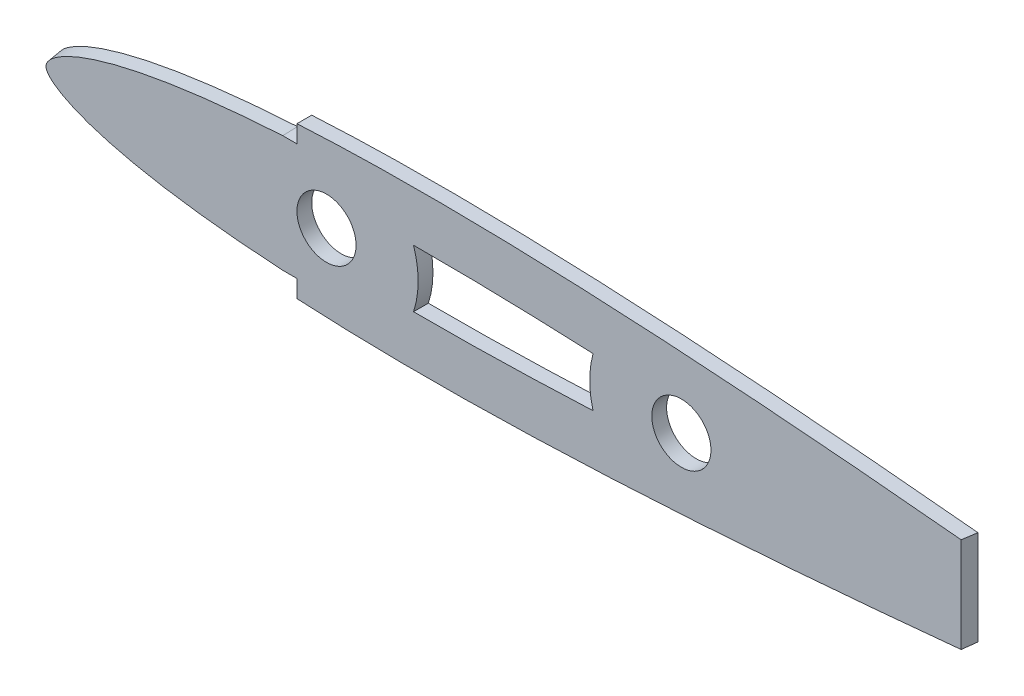
SolidWorks part; units mm, degrees
material "Balsa"
ref_plane "Front Plane" through (0, 0, 0) normal (0, 0, 1) x (1, 0, 0)
ref_plane "Top Plane" through (0, 0, 0) normal (0, 1, 0) x (1, 0, 0)
ref_plane "Right Plane" through (0, 0, 0) normal (1, 0, 0) x (0, 0, -1)
curve "Curve1"
  spline degree 3 poles (283.1769, -0.4783, 0) (283.1769, 0.4783, 0) (282.223, 0.3615, 0) (281.0143, 0.7018, 0) (278.7977, 0.9121, 0) (275.8116, 1.3634, 0) (271.9651, 1.8671, 0) (267.3264, 2.4878, 0) (261.9077, 3.1895, 0) (255.7482, 3.9707, 0) (248.8838, 4.8179, 0) (241.3575, 5.7194, 0) (233.2156, 6.6641, 0) (224.5081, 7.6392, 0) (215.289, 8.6327, 0) (205.6149, 9.6324, 0) (195.5456, 10.6252, 0) (185.1431, 11.5974, 0) (174.4716, 12.536, 0) (163.5969, 13.4255, 0) (152.5858, 14.2512, 0) (141.5064, 14.998, 0) (130.4269, 15.6501, 0) (119.4155, 16.1911, 0) (108.5401, 16.6066, 0) (97.8677, 16.883, 0) (87.464, 17.0069, 0) (77.3931, 16.9683, 0) (67.717, 16.7598, 0) (58.4953, 16.3762, 0) (49.7847, 15.8164, 0) (41.6389, 15.0822, 0) (34.1075, 14.1792, 0) (27.2365, 13.1151, 0) (21.0677, 11.9011, 0) (15.637, 10.5509, 0) (10.9755, 9.0777, 0) (7.1067, 7.4951, 0) (4.043, 5.8139, 0) (1.7891, 4.0308, 0) (0.3455, 2.1026, 0) (-0.161, 0, 0) (0.3455, -2.1026, 0) (1.7891, -4.0308, 0) (4.043, -5.8139, 0) (7.1067, -7.4951, 0) (10.9755, -9.0777, 0) (15.637, -10.5509, 0) (21.0677, -11.9011, 0) (27.2365, -13.1151, 0) (34.1075, -14.1792, 0) (41.6389, -15.0822, 0) (49.7847, -15.8164, 0) (58.4953, -16.3762, 0) (67.717, -16.7598, 0) (77.3931, -16.9683, 0) (87.464, -17.0069, 0) (97.8677, -16.883, 0) (108.5401, -16.6066, 0) (119.4155, -16.1911, 0) (130.4269, -15.6501, 0) (141.5064, -14.998, 0) (152.5858, -14.2512, 0) (163.5969, -13.4255, 0) (174.4716, -12.536, 0) (185.1431, -11.5974, 0) (195.5456, -10.6252, 0) (205.6149, -9.6324, 0) (215.289, -8.6327, 0) (224.5081, -7.6392, 0) (233.2156, -6.6641, 0) (241.3575, -5.7194, 0) (248.8838, -4.8179, 0) (255.7482, -3.9707, 0) (261.9077, -3.1895, 0) (267.3264, -2.4878, 0) (271.9651, -1.8671, 0) (275.8116, -1.3634, 0) (278.7977, -0.9121, 0) (281.0143, -0.7018, 0) (282.223, -0.3615, 0) (283.1769, -0.4783, 0) (283.1769, 0.4783, 0) (282.223, 0.3615, 0) knots -0.004279 -0.001997 -0.001234 0 0.000762 0.003045 0.006832 0.012101 0.018818 0.026939 0.036415 0.047185 0.05918 0.072328 0.086544 0.101741 0.117823 0.134691 0.15224 0.170361 0.188941 0.207865 0.227016 0.246276 0.265525 0.284645 0.30352 0.322035 0.340078 0.357543 0.374325 0.39033 0.405464 0.419644 0.432793 0.444844 0.455738 0.465429 0.473886 0.481102 0.487102 0.491975 0.495931 0.499383 0.502835 0.50679 0.511664 0.517664 0.524879 0.533337 0.543028 0.553922 0.565972 0.579122 0.593302 0.608436 0.62444 0.641223 0.658687 0.676731 0.695245 0.714121 0.733241 0.75249 0.77175 0.7909 0.809825 0.828404 0.846525 0.864074 0.880942 0.897025 0.912222 0.926438 0.939585 0.951581 0.962351 0.971826 0.979948 0.986664 0.991933 0.995721 0.998003 0.998766 1 1.000762 1.003045 1.006832 periodic
sketch "Sketch1" plane through (0, 0, 0) normal (0, 0, 1) x (1, 0, 0)
  spline S0 degree 3 poles (283.1769, -0.4783) (283.1769, 0.4783) (282.223, 0.3615) (281.0143, 0.7018) (278.7977, 0.9121) (275.8116, 1.3634) (271.9651, 1.8671) (267.3264, 2.4878) (261.9077, 3.1895) (255.7482, 3.9707) (248.8838, 4.8179) (241.3575, 5.7194) (233.2156, 6.6641) (224.5081, 7.6392) (215.289, 8.6327) (205.6149, 9.6324) (195.5456, 10.6252) (185.1431, 11.5974) (174.4716, 12.536) (163.5969, 13.4255) (152.5858, 14.2512) (141.5064, 14.998) (130.4269, 15.6501) (119.4155, 16.1911) (108.5401, 16.6066) (97.8677, 16.883) (87.464, 17.0069) (77.3931, 16.9683) (67.717, 16.7598) (58.4953, 16.3762) (49.7847, 15.8164) (41.6389, 15.0822) (34.1075, 14.1792) (27.2365, 13.1151) (21.0677, 11.9011) (15.637, 10.5509) (10.9755, 9.0777) (7.1067, 7.4951) (4.043, 5.8139) (1.7891, 4.0308) (0.3455, 2.1026) (-0.161, 0) (0.3455, -2.1026) (1.7891, -4.0308) (4.043, -5.8139) (7.1067, -7.4951) (10.9755, -9.0777) (15.637, -10.5509) (21.0677, -11.9011) (27.2365, -13.1151) (34.1075, -14.1792) (41.6389, -15.0822) (49.7847, -15.8164) (58.4953, -16.3762) (67.717, -16.7598) (77.3931, -16.9683) (87.464, -17.0069) (97.8677, -16.883) (108.5401, -16.6066) (119.4155, -16.1911) (130.4269, -15.6501) (141.5064, -14.998) (152.5858, -14.2512) (163.5969, -13.4255) (174.4716, -12.536) (185.1431, -11.5974) (195.5456, -10.6252) (205.6149, -9.6324) (215.289, -8.6327) (224.5081, -7.6392) (233.2156, -6.6641) (241.3575, -5.7194) (248.8838, -4.8179) (255.7482, -3.9707) (261.9077, -3.1895) (267.3264, -2.4878) (271.9651, -1.8671) (275.8116, -1.3634) (278.7977, -0.9121) (281.0143, -0.7018) (282.223, -0.3615) (283.1769, -0.4783) (283.1769, 0.4783) (282.223, 0.3615) knots -0.004279 -0.001997 -0.001234 0 0.000762 0.003045 0.006832 0.012101 0.018818 0.026939 0.036415 0.047185 0.05918 0.072328 0.086544 0.101741 0.117823 0.134691 0.15224 0.170361 0.188941 0.207865 0.227016 0.246276 0.265525 0.284645 0.30352 0.322035 0.340078 0.357543 0.374325 0.39033 0.405464 0.419644 0.432793 0.444844 0.455738 0.465429 0.473886 0.481102 0.487102 0.491975 0.495931 0.499383 0.502835 0.50679 0.511664 0.517664 0.524879 0.533337 0.543028 0.553922 0.565972 0.579122 0.593302 0.608436 0.62444 0.641223 0.658687 0.676731 0.695245 0.714121 0.733241 0.75249 0.77175 0.7909 0.809825 0.828404 0.846525 0.864074 0.880942 0.897025 0.912222 0.926438 0.939585 0.951581 0.962351 0.971826 0.979948 0.986664 0.991933 0.995721 0.998003 0.998766 1 1.000762 1.003045 1.006832 only from (283.0068, 0.3566) to (283.0068, 0.3566) construction
  spline S1 degree 3 poles (283.1769, -0.4783) (283.1769, 0.4783) (282.223, 0.3615) (281.0143, 0.7018) (278.7977, 0.9121) (275.8116, 1.3634) (271.9651, 1.8671) (267.3264, 2.4878) (261.9077, 3.1895) (255.7482, 3.9707) (248.8838, 4.8179) (241.3575, 5.7194) (233.2156, 6.6641) (224.5081, 7.6392) (215.289, 8.6327) (205.6149, 9.6324) (195.5456, 10.6252) (185.1431, 11.5974) (174.4716, 12.536) (163.5969, 13.4255) (152.5858, 14.2512) (141.5064, 14.998) (130.4269, 15.6501) (119.4155, 16.1911) (108.5401, 16.6066) (97.8677, 16.883) (87.464, 17.0069) (77.3931, 16.9683) (67.717, 16.7598) (58.4953, 16.3762) (49.7847, 15.8164) (41.6389, 15.0822) (34.1075, 14.1792) (27.2365, 13.1151) (21.0677, 11.9011) (15.637, 10.5509) (10.9755, 9.0777) (7.1067, 7.4951) (4.043, 5.8139) (1.7891, 4.0308) (0.3455, 2.1026) (-0.161, 0) (0.3455, -2.1026) (1.7891, -4.0308) (4.043, -5.8139) (7.1067, -7.4951) (10.9755, -9.0777) (15.637, -10.5509) (21.0677, -11.9011) (27.2365, -13.1151) (34.1075, -14.1792) (41.6389, -15.0822) (49.7847, -15.8164) (58.4953, -16.3762) (67.717, -16.7598) (77.3931, -16.9683) (87.464, -17.0069) (97.8677, -16.883) (108.5401, -16.6066) (119.4155, -16.1911) (130.4269, -15.6501) (141.5064, -14.998) (152.5858, -14.2512) (163.5969, -13.4255) (174.4716, -12.536) (185.1431, -11.5974) (195.5456, -10.6252) (205.6149, -9.6324) (215.289, -8.6327) (224.5081, -7.6392) (233.2156, -6.6641) (241.3575, -5.7194) (248.8838, -4.8179) (255.7482, -3.9707) (261.9077, -3.1895) (267.3264, -2.4878) (271.9651, -1.8671) (275.8116, -1.3634) (278.7977, -0.9121) (281.0143, -0.7018) (282.223, -0.3615) (283.1769, -0.4783) (283.1769, 0.4783) (282.223, 0.3615) knots -0.004279 -0.001997 -0.001234 0 0.000762 0.003045 0.006832 0.012101 0.018818 0.026939 0.036415 0.047185 0.05918 0.072328 0.086544 0.101741 0.117823 0.134691 0.15224 0.170361 0.188941 0.207865 0.227016 0.246276 0.265525 0.284645 0.30352 0.322035 0.340078 0.357543 0.374325 0.39033 0.405464 0.419644 0.432793 0.444844 0.455738 0.465429 0.473886 0.481102 0.487102 0.491975 0.495931 0.499383 0.502835 0.50679 0.511664 0.517664 0.524879 0.533337 0.543028 0.553922 0.565972 0.579122 0.593302 0.608436 0.62444 0.641223 0.658687 0.676731 0.695245 0.714121 0.733241 0.75249 0.77175 0.7909 0.809825 0.828404 0.846525 0.864074 0.880942 0.897025 0.912222 0.926438 0.939585 0.951581 0.962351 0.971826 0.979948 0.986664 0.991933 0.995721 0.998003 0.998766 1 1.000762 1.003045 1.006832 only from (283.0068, 0.3566) to (283.0068, 0.3566)
extrude "Boss-Extrude1" add sketch "Sketch1" along normal blind 3.175
sketch "Sketch2" plane through (0, 0, 3.175) normal (0, 0, 1) x (1, 0, 0)
  circle A0 centre (63.5, 0) radius 6.35
  circle A1 centre (139.7, 0) radius 6.35
  dimension "D1" = 12.7
  dimension "D2" = 12.7
  dimension "D3" = 0
  dimension "D4" = 0
  dimension "D5" = 63.5
  dimension "D6" = 139.7
extrude "Cut-Extrude1" cut sketch "Sketch2" against normal blind 3.175
sketch "Sketch3" plane through (0, 0, 0) normal (0, 1, 0) x (1, 0, 0)
  line L2 (200.2201, 0) -> (199.7735, -3.175)
  line L8 (283.1344, -3.175) -> (283.1344, 0) construction
  line L9 (283.1344, -3.175) -> (283.1344, 0)
  line L10 (199.7735, -3.175) -> (283.1344, -3.175)
extrude "Cut-Extrude2" cut sketch "Sketch3" against normal through all both and the other way through all
sketch "Sketch4" plane through (0, 0, 0) normal (0, 0, -1) x (-1, 0, 0)
  line L0 (-57.15, -15.9311) -> (-57.15, -12.6144)
  line L1 (-57.15, -15.9311) -> (-57.15, -12.6144)
  line L2 (-54.102, -12.6144) -> (-57.15, -12.6144)
  line L3 (-54.102, -12.6144) -> (-57.15, -12.6144)
  line L4 (-57.15, 12.6144) -> (-57.15, 15.9311)
  line L5 (-57.15, 12.6144) -> (-57.15, 15.9311)
  line L6 (-57.15, 12.6144) -> (-54.102, 12.6144)
  line L7 (-57.15, 12.6144) -> (-54.102, 12.6144)
  line L9 (16.291, 29.4613) -> (3.1074, -36.0979)
  line L11 (-57.15, -15.9311) -> (-57.15, -26.911)
  line L12 (-57.15, -26.911) -> (3.1074, -36.0979)
  line L13 (-57.15, 15.9311) -> (-57.15, 23.7689)
  line L14 (-57.15, 23.7689) -> (16.291, 29.4613)
  spline S0 degree 3 poles (1603.9477, 1127.4313) (-409.4491, -100.2252) (-222.7052, 25.2394) (-46.8504, 12.1195) (-43.234, 11.8063) (-39.6271, 11.4462) (-36.0313, 11.0349) (-32.4506, 10.5661) (-28.886, 10.0331) (-25.9367, 9.528) (-23.5902, 9.0821) (-21.8403, 8.725) (-20.101, 8.3428) (-18.3748, 7.9334) (-16.663, 7.4946) (-14.9702, 7.0233) (-13.3008, 6.5163) (-11.6611, 5.9687) (-10.0604, 5.3771) (-8.5083, 4.731) (-7.0229, 4.0237) (-5.6385, 3.2547) (-4.6091, 2.5577) (-3.9035, 1.9678) (-3.4556, 1.5205) (-3.0957, 1.0697) (-2.8713, 0.6793) (-2.7459, 0.308) (-2.7091, 0) (-2.7459, -0.308) (-2.8713, -0.6793) (-3.0958, -1.0697) (-3.4556, -1.5205) (-3.9035, -1.9678) (-4.6094, -2.5579) (-5.6383, -3.2546) (-7.023, -4.0238) (-8.5083, -4.731) (-10.0604, -5.3771) (-11.6611, -5.9687) (-13.3008, -6.5163) (-14.9701, -7.0232) (-16.663, -7.4946) (-18.3748, -7.9334) (-20.101, -8.3428) (-21.8403, -8.725) (-23.5902, -9.0821) (-25.9368, -9.528) (-28.8859, -10.0331) (-32.4506, -10.5661) (-36.0313, -11.0349) (-39.6271, -11.4462) (-43.234, -11.8063) (-46.8504, -12.1195) (-222.1359, -25.197) (-408.2838, 99.3983) (1617.0872, -1107.8528) knots -4.455305 -4.455305 -4.455305 -4.455305 0.03125 0.0625 0.09375 0.125 0.15625 0.1875 0.21875 0.25 0.265625 0.28125 0.296875 0.3125 0.328125 0.34375 0.359375 0.375 0.390625 0.40625 0.421875 0.4375 0.453125 0.460938 0.46875 0.476562 0.484375 0.492188 0.5 0.507812 0.515625 0.523438 0.53125 0.539062 0.546875 0.5625 0.578125 0.59375 0.609375 0.625 0.640625 0.65625 0.671875 0.6875 0.703125 0.71875 0.734375 0.75 0.78125 0.8125 0.84375 0.875 0.90625 0.9375 0.96875 5.440565 5.440565 5.440565 5.440565 only from (-54.102, 12.6144) to (-54.102, -12.6144)
  spline S1 degree 3 poles (-54.102, 12.6144) (-52.893, 12.5437) (-50.4746, 12.3899) (-46.8504, 12.1195) (-43.234, 11.8063) (-39.6271, 11.4462) (-36.0313, 11.0349) (-32.4506, 10.5661) (-28.886, 10.0331) (-25.9367, 9.528) (-23.5902, 9.0821) (-21.8403, 8.725) (-20.101, 8.3428) (-18.3748, 7.9334) (-16.663, 7.4946) (-14.9702, 7.0233) (-13.3008, 6.5163) (-11.6611, 5.9687) (-10.0604, 5.3771) (-8.5083, 4.731) (-7.0229, 4.0237) (-5.6385, 3.2547) (-4.6091, 2.5577) (-3.9035, 1.9678) (-3.4556, 1.5205) (-3.0957, 1.0697) (-2.8713, 0.6793) (-2.7459, 0.308) (-2.7091, 0) (-2.7459, -0.308) (-2.8713, -0.6793) (-3.0958, -1.0697) (-3.4556, -1.5205) (-3.9035, -1.9678) (-4.6094, -2.5579) (-5.6383, -3.2546) (-7.023, -4.0238) (-8.5083, -4.731) (-10.0604, -5.3771) (-11.6611, -5.9687) (-13.3008, -6.5163) (-14.9701, -7.0232) (-16.663, -7.4946) (-18.3748, -7.9334) (-20.101, -8.3428) (-21.8403, -8.725) (-23.5902, -9.0821) (-25.9368, -9.528) (-28.8859, -10.0331) (-32.4506, -10.5661) (-36.0313, -11.0349) (-39.6271, -11.4462) (-43.234, -11.8063) (-46.8504, -12.1195) (-50.4745, -12.3899) (-52.893, -12.5437) (-54.102, -12.6144) knots 0 0 0 0 0.03125 0.0625 0.09375 0.125 0.15625 0.1875 0.21875 0.25 0.265625 0.28125 0.296875 0.3125 0.328125 0.34375 0.359375 0.375 0.390625 0.40625 0.421875 0.4375 0.453125 0.460938 0.46875 0.476562 0.484375 0.492188 0.5 0.507812 0.515625 0.523438 0.53125 0.539062 0.546875 0.5625 0.578125 0.59375 0.609375 0.625 0.640625 0.65625 0.671875 0.6875 0.703125 0.71875 0.734375 0.75 0.78125 0.8125 0.84375 0.875 0.90625 0.9375 0.96875 1 1 1 1
sketch "Sketch5" plane through (0, 0, 3.175) normal (0, 0, 1) x (1, 0, 0)
  line L0 (57.15, -15.8407) -> (57.15, -12.5178)
  line L1 (57.15, -15.8407) -> (57.15, -12.5178)
  line L2 (54.102, -12.5178) -> (57.15, -12.5178)
  line L3 (54.102, -12.5178) -> (57.15, -12.5178)
  line L4 (57.15, 12.5178) -> (57.15, 15.8407)
  line L5 (57.15, 12.5178) -> (57.15, 15.8407)
  line L6 (57.15, 12.5178) -> (54.102, 12.5178)
  line L7 (57.15, 12.5178) -> (54.102, 12.5178)
  line L9 (-13.6603, 32.1968) -> (4.7514, -35.9264)
  line L11 (57.15, 15.8407) -> (57.15, 24.5287)
  line L12 (57.15, 24.5287) -> (-13.6603, 32.1968)
  line L13 (57.15, -15.8407) -> (57.15, -29.0129)
  line L14 (57.15, -29.0129) -> (4.7514, -35.9264)
  spline S0 degree 3 poles (-1613.5734, 1113.0651) (405.921, -99.1234) (220.9953, 25.1428) (46.923, 12.0225) (43.3429, 11.7096) (39.7723, 11.3502) (36.213, 10.9401) (32.6687, 10.4731) (29.1406, 9.9424) (26.2217, 9.4398) (23.8996, 8.9963) (22.1681, 8.6412) (20.4471, 8.2613) (18.7392, 7.8544) (17.0458, 7.4185) (15.3713, 6.9503) (13.7204, 6.447) (12.0991, 5.9036) (10.5167, 5.3168) (8.9829, 4.6764) (7.5154, 3.9756) (6.1484, 3.2144) (5.1324, 2.5254) (4.4363, 1.9426) (3.9945, 1.5009) (3.6396, 1.0557) (3.4182, 0.6703) (3.2945, 0.3038) (3.2583, 0) (3.2945, -0.3038) (3.4182, -0.6703) (3.6396, -1.0557) (3.9945, -1.5009) (4.4363, -1.9426) (5.1328, -2.5256) (6.1482, -3.2142) (7.5155, -3.9757) (8.9829, -4.6763) (10.5168, -5.3169) (12.0991, -5.9036) (13.7204, -6.447) (15.3713, -6.9503) (17.0458, -7.4185) (18.7392, -7.8544) (20.4471, -8.2613) (22.1681, -8.6412) (23.8996, -8.9963) (26.2218, -9.4398) (29.1405, -9.9424) (32.6687, -10.4731) (36.2129, -10.9401) (39.7723, -11.3502) (43.3429, -11.7096) (46.923, -12.0225) (220.4075, -25.0986) (404.7164, 98.2692) (-1626.8557, -1092.8409) knots -4.454752 -4.454752 -4.454752 -4.454752 0.03125 0.0625 0.09375 0.125 0.15625 0.1875 0.21875 0.25 0.265625 0.28125 0.296875 0.3125 0.328125 0.34375 0.359375 0.375 0.390625 0.40625 0.421875 0.4375 0.453125 0.460938 0.46875 0.476562 0.484375 0.492188 0.5 0.507812 0.515625 0.523438 0.53125 0.539062 0.546875 0.5625 0.578125 0.59375 0.609375 0.625 0.640625 0.65625 0.671875 0.6875 0.703125 0.71875 0.734375 0.75 0.78125 0.8125 0.84375 0.875 0.90625 0.9375 0.96875 5.439378 5.439378 5.439378 5.439378 only from (54.102, 12.5178) to (54.102, -12.5178)
  spline S1 degree 3 poles (54.102, 12.5178) (52.9051, 12.4469) (50.5109, 12.2929) (46.923, 12.0225) (43.3429, 11.7096) (39.7723, 11.3502) (36.213, 10.9401) (32.6687, 10.4731) (29.1406, 9.9424) (26.2217, 9.4398) (23.8996, 8.9963) (22.1681, 8.6412) (20.4471, 8.2613) (18.7392, 7.8544) (17.0458, 7.4185) (15.3713, 6.9503) (13.7204, 6.447) (12.0991, 5.9036) (10.5167, 5.3168) (8.9829, 4.6764) (7.5154, 3.9756) (6.1484, 3.2144) (5.1324, 2.5254) (4.4363, 1.9426) (3.9945, 1.5009) (3.6396, 1.0557) (3.4182, 0.6703) (3.2945, 0.3038) (3.2583, 0) (3.2945, -0.3038) (3.4182, -0.6703) (3.6396, -1.0557) (3.9945, -1.5009) (4.4363, -1.9426) (5.1328, -2.5256) (6.1482, -3.2142) (7.5155, -3.9757) (8.9829, -4.6763) (10.5168, -5.3169) (12.0991, -5.9036) (13.7204, -6.447) (15.3713, -6.9503) (17.0458, -7.4185) (18.7392, -7.8544) (20.4471, -8.2613) (22.1681, -8.6412) (23.8996, -8.9963) (26.2218, -9.4398) (29.1405, -9.9424) (32.6687, -10.4731) (36.2129, -10.9401) (39.7723, -11.3502) (43.3429, -11.7096) (46.923, -12.0225) (50.5109, -12.2929) (52.9051, -12.4469) (54.102, -12.5178) knots 0 0 0 0 0.03125 0.0625 0.09375 0.125 0.15625 0.1875 0.21875 0.25 0.265625 0.28125 0.296875 0.3125 0.328125 0.34375 0.359375 0.375 0.390625 0.40625 0.421875 0.4375 0.453125 0.460938 0.46875 0.476562 0.484375 0.492188 0.5 0.507812 0.515625 0.523438 0.53125 0.539062 0.546875 0.5625 0.578125 0.59375 0.609375 0.625 0.640625 0.65625 0.671875 0.6875 0.703125 0.71875 0.734375 0.75 0.78125 0.8125 0.84375 0.875 0.90625 0.9375 0.96875 1 1 1 1
loft "Cut-Loft1" cut profiles "Sketch5", "Sketch4"
sketch "Sketch6" plane through (0, 0, 0) normal (0, 0, -1) x (-1, 0, 0)
  arc A4 (-120.7437, -5.3063) -> (-120.7437, 5.3063) centre (-139.7, 0) ccw
  arc A6 (-82.1883, 6.1845) -> (-82.1883, -6.1845) centre (-63.5, 0) ccw
  spline S5 degree 3 poles (-120.7437, 5.3063) (-116.114, 5.5168) (-111.4868, 5.6956) (-101.374, 6.0042) (-95.8907, 6.1186) (-87.6714, 6.1897) (-84.9282, 6.1967) (-82.1883, 6.1845) knots 0.519742 0.519742 0.519742 0.519742 0.625 0.625 0.75 0.75 0.812699 0.812699 0.812699 0.812699
  spline S9 degree 3 poles (-82.1883, -6.1845) (-84.9282, -6.1967) (-87.6714, -6.1897) (-95.8907, -6.1186) (-101.374, -6.0042) (-111.4868, -5.6956) (-116.114, -5.5168) (-120.7437, -5.3063) knots 0.187301 0.187301 0.187301 0.187301 0.25 0.25 0.375 0.375 0.480258 0.480258 0.480258 0.480258
extrude "Cut-Extrude3" cut sketch "Sketch6" against normal blind 7.62
